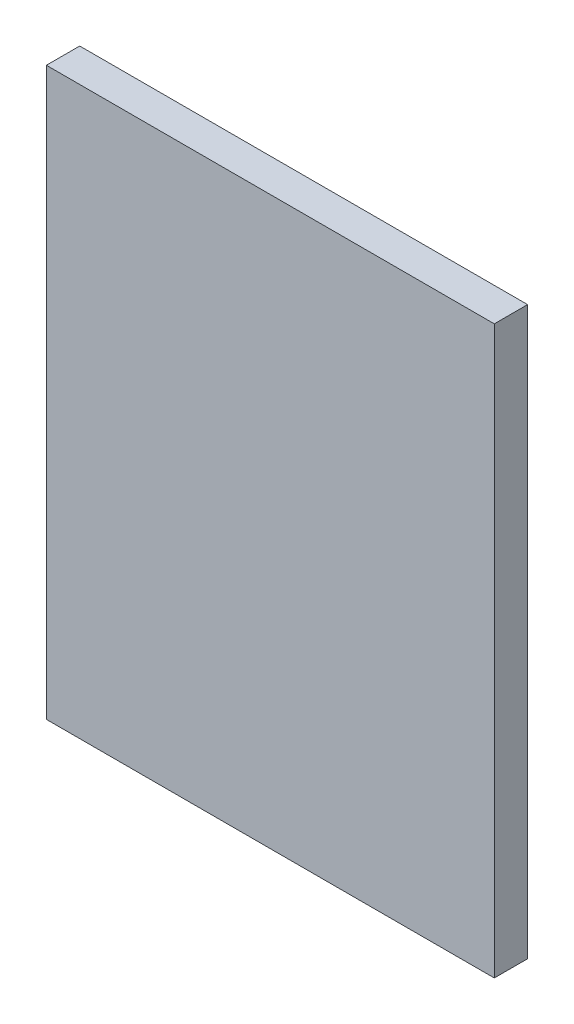
SolidWorks part; units mm, degrees
ref_plane "Front Plane" through (0, 0, 0) normal (0, 0, 1) x (1, 0, 0)
ref_plane "Top Plane" through (0, 0, 0) normal (0, 1, 0) x (1, 0, 0)
ref_plane "Right Plane" through (0, 0, 0) normal (1, 0, 0) x (0, 0, -1)
sketch "Sketch2" plane through (0, 0, 0) normal (0, 0, 1) x (1, 0, 0)
  line L1 (-21.336, -26.9875) -> (21.336, -26.9875)
  line L2 (-21.336, -26.9875) -> (-21.336, 26.9875)
  line L3 (-21.336, 26.9875) -> (21.336, 26.9875)
  line L4 (21.336, -26.9875) -> (21.336, 26.9875)
  line L5 (-21.336, -26.9875) -> (21.336, 26.9875) construction
  line L6 (-21.336, 26.9875) -> (21.336, -26.9875) construction
  point P0 (0, 0)
  dimension "D1" = 42.672
  dimension "D2" = 53.975
extrude "Boss-Extrude1" add sketch "Sketch2" along normal mid plane 3.175
